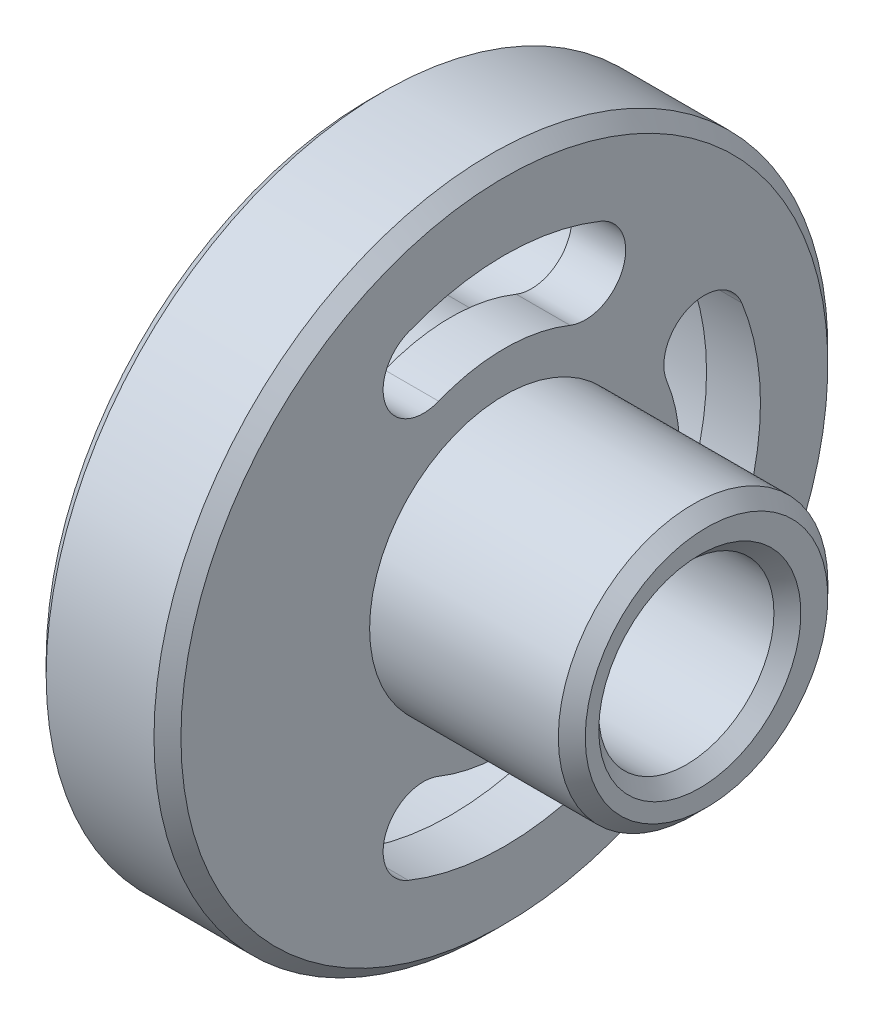
SolidWorks part; units mm, degrees
ref_plane "Спереди" through (0, 0, 0) normal (0, 0, 1) x (1, 0, 0)
ref_plane "Сверху" through (0, 0, 0) normal (0, 1, 0) x (1, 0, 0)
ref_plane "Справа" through (0, 0, 0) normal (1, 0, 0) x (0, 0, -1)
other "Configuration Table"
sketch "Эскиз1" plane through (0, 0, 0) normal (0, 0, 1) x (1, 0, 0)
  line L6 (0, 0) -> (24.4592, 0) construction
  line L7 (0, 0) -> (0, 24)
  line L8 (1, 25) -> (9, 25)
  line L9 (10, 24) -> (10, 10)
  line L10 (10, 10) -> (24, 10)
  line L11 (25, 9) -> (25, 0)
  line L12 (25, 0) -> (0, 0)
  line L13 (0, 24) -> (1, 25)
  line L14 (9, 25) -> (10, 24)
  line L15 (24, 10) -> (25, 9)
  point P4 (0, 25)
  point P5 (10, 25)
  point P7 (25, 10)
  dimension "D1" = 20
  dimension "D2" = 50
  dimension "D3" = 10
  dimension "D4" = 25
revolve "Повернуть1" add sketch "Эскиз1" angle 360 about L6
sketch "Эскиз3" plane through (25, 0, 0) normal (1, 0, 0) x (0, 0, -1)
  line L0 (0, 0) -> (8.7913, 0) construction
  circle A0 centre (-0.5, 0) radius 6.5
  dimension "D1" = 13
  dimension "D2" = 0.5
sketch "Эскиз4" plane through (0, 0, 0) normal (-1, 0, 0) x (0, 0, 1)
  line L0 (-8.7913, 0) -> (27.3062, 0) construction
  line L1 (0, 0) -> (0, 21.7955) construction
  line L2 (0, 0) -> (4.125, 10.1973) construction
  arc A0 (6, 14.8324) -> (-6, 14.8324) centre (0, 0) ccw construction
  arc A5 (7.875, 19.4675) -> (-7.875, 19.4675) centre (0, 0) ccw
  arc A6 (4.125, 10.1973) -> (-4.125, 10.1973) centre (0, 0) ccw
  arc A7 (4.125, 10.1973) -> (7.875, 19.4675) centre (6, 14.8324) ccw
  arc A8 (-7.875, 19.4675) -> (-4.125, 10.1973) centre (-6, 14.8324) ccw
  arc A9 (-10.1973, 4.125) -> (-10.1973, -4.125) centre (0, 0) ccw
  arc A10 (-10.1973, 4.125) -> (-19.4675, 7.875) centre (-14.8324, 6) ccw
  arc A11 (-19.4675, -7.875) -> (-10.1973, -4.125) centre (-14.8324, -6) ccw
  arc A12 (-19.4675, 7.875) -> (-19.4675, -7.875) centre (0, 0) ccw
  arc A13 (-14.8324, 6) -> (-14.8324, -6) centre (0, 0) ccw construction
  arc A14 (-4.125, -10.1973) -> (4.125, -10.1973) centre (0, 0) ccw
  arc A15 (-4.125, -10.1973) -> (-7.875, -19.4675) centre (-6, -14.8324) ccw
  arc A16 (7.875, -19.4675) -> (4.125, -10.1973) centre (6, -14.8324) ccw
  arc A17 (-7.875, -19.4675) -> (7.875, -19.4675) centre (0, 0) ccw
  arc A18 (-6, -14.8324) -> (6, -14.8324) centre (0, 0) ccw construction
  point P3 (-54.8052, 25.1622)
  point P4 (0, 16)
  point P20 (-16, 0)
  point P27 (0, -16)
  dimension "D1" = 5
  dimension "D4" = 6
  dimension "D3" = 6
  dimension "D5" = 90
  dimension "D7" = 11
  dimension "D6" = 3
extrude "Вырез-Вытянуть2" cut sketch "Эскиз4" against normal blind 6
sketch "Эскиз5" plane through (0, 0, 0) normal (-1, 0, 0) x (0, 0, 1)
  line L0 (0, 0) -> (0, 21.7955) construction
  line L1 (0, 0) -> (4.875, 12.0513) construction
  arc A0 (6, 14.8324) -> (-6, 14.8324) centre (0, 0) ccw construction
  arc A1 (6, 14.8324) -> (-6, 14.8324) centre (0, 0) ccw construction
  arc A2 (7.125, 17.6135) -> (-7.125, 17.6135) centre (0, 0) ccw
  arc A3 (4.875, 12.0513) -> (-4.875, 12.0513) centre (0, 0) ccw
  arc A4 (4.875, 12.0513) -> (7.125, 17.6135) centre (6, 14.8324) ccw
  arc A5 (-7.125, 17.6135) -> (-4.875, 12.0513) centre (-6, 14.8324) ccw
  arc A6 (-12.0513, 4.875) -> (-12.0513, -4.875) centre (0, 0) ccw
  arc A7 (-12.0513, 4.875) -> (-17.6135, 7.125) centre (-14.8324, 6) ccw
  arc A8 (-17.6135, -7.125) -> (-12.0513, -4.875) centre (-14.8324, -6) ccw
  arc A9 (-17.6135, 7.125) -> (-17.6135, -7.125) centre (0, 0) ccw
  arc A10 (-14.8324, 6) -> (-14.8324, -6) centre (0, 0) ccw construction
  arc A11 (-4.875, -12.0513) -> (4.875, -12.0513) centre (0, 0) ccw
  arc A12 (-4.875, -12.0513) -> (-7.125, -17.6135) centre (-6, -14.8324) ccw
  arc A13 (7.125, -17.6135) -> (4.875, -12.0513) centre (6, -14.8324) ccw
  arc A14 (-7.125, -17.6135) -> (7.125, -17.6135) centre (0, 0) ccw
  arc A15 (-6, -14.8324) -> (6, -14.8324) centre (0, 0) ccw construction
  point P8 (0, 16)
  point P19 (-16, 0)
  point P26 (0, -16)
  dimension "D1" = 3
  dimension "D2" = 6
  dimension "D3" = 3
extrude "Вырез-Вытянуть3" cut sketch "Эскиз5" against normal through all
extrude "Вырез-Вытянуть4" cut sketch "Эскиз3" against normal through all contours A0
chamfer "Фаска1" distance 1 angle 45 1 edges at (25, 0, -6)
chamfer "Фаска3" distance 1 angle 45 1 edges at (0, 0, -6)
